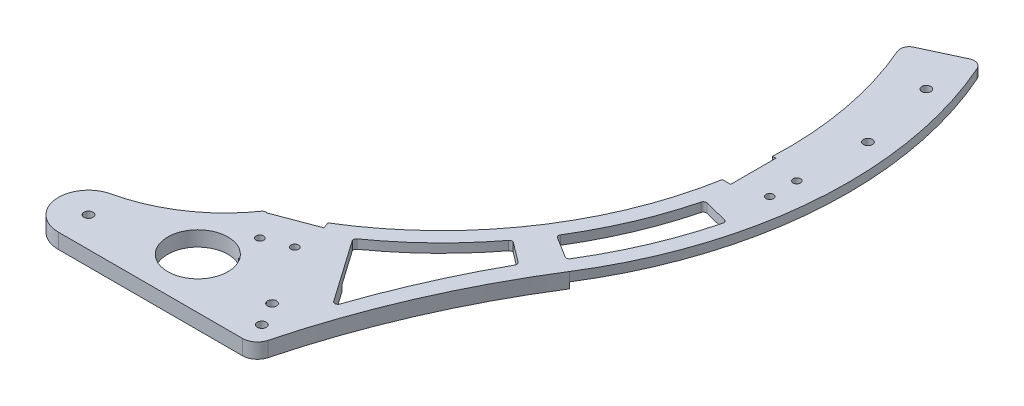
SolidWorks part; units mm, degrees
ref_plane "前视基准面" through (0, 0, 0) normal (0, 0, 1) x (1, 0, 0)
ref_plane "上视基准面" through (0, 0, 0) normal (0, 1, 0) x (1, 0, 0)
ref_plane "右视基准面" through (0, 0, 0) normal (1, 0, 0) x (0, 0, -1)
other "Configuration Table"
sketch "草图1" plane through (0, 0, 0) normal (0, 1, 0) x (1, 0, 0)
  line L0 (0, 0) -> (0, -135)
  line L1 (0, 0) -> (122.3516, 57.0535)
  line L2 (0, 0) -> (125, 0) construction
  arc A1 (0, -135) -> (122.3516, 57.0535) centre (0, 0) ccw
  dimension "D1" = 135
  dimension "D2" = 25
extrude "凸台-拉伸1" add sketch "草图1" along normal blind 3
sketch "草图2" plane through (0, 3, 0) normal (0, 1, 0) x (1, 0, 0)
  line L1 (0, 0) -> (104.2254, 48.6011)
  line L2 (122.3516, 57.0535) -> (0, 0) construction
  line L3 (0, 0) -> (54, -123.7295) construction
  line L4 (54, -123.7295) -> (46, -105.3992)
  line L5 (30, -68.7386) -> (0, -68.7386) construction
  line L7 (0, 0) -> (0, -135)
  arc A0 (46, -105.3992) -> (104.2254, 48.6011) centre (0, 0) ccw
  arc A1 (0, -135) -> (122.3516, 57.0535) centre (0, 0) ccw construction
  arc A2 (30, -68.7386) -> (67.9731, 31.6964) centre (0, 0) ccw construction
  arc A3 (0, -135) -> (54, -123.7295) centre (0, 0) ccw
  dimension "D1" = 115
  dimension "D4" = 75
  dimension "D2" = 30
extrude "切除-拉伸1" cut sketch "草图2" against normal blind 5
sketch "草图3" plane through (0, 3, 0) normal (0, 1, 0) x (1, 0, 0)
  line L0 (46, -105.3992) -> (54, -123.7295)
  line L1 (83.097, -145.3992) -> (18.097, -145.3992)
  line L2 (61.9303, -96.9001) -> (83.097, -145.3992) construction
  line L3 (8.097, -135.3992) -> (8.097, -145.3992) construction
  arc A0 (15.9052, -125.6424) -> (46, -105.3992) centre (4.9463, -76.8582) ccw
  arc A1 (15.9052, -125.6424) -> (18.097, -145.3992) centre (18.097, -135.3992) ccw
  arc A2 (114.2738, -71.8784) -> (83.097, -145.3992) centre (325.8919, -204.9864) ccw
  arc A4 (54, -123.7295) -> (114.2738, -71.8784) centre (0, 0) ccw
  arc A5 (54, -123.7295) -> (122.3516, 57.0535) centre (0, 0) ccw construction
  arc A6 (46, -105.3992) -> (104.2254, 48.6011) centre (0, 0) ccw construction
  dimension "D1" = 10
  dimension "D2" = 50
  dimension "D5" = 250
  dimension "D3" = 40
  dimension "D4" = 75
  dimension "D6" = 18
extrude "凸台-拉伸2" add sketch "草图3" against normal blind 5
sketch "草图4" plane through (0, 3, 0) normal (0, 1, 0) x (1, 0, 0)
  line L0 (0, 0) -> (135, 0) construction
  line L1 (59.9011, -97.2428) -> (60.96, -100.0497)
  line L2 (113, -5) -> (116, -5)
  line L3 (113, -5) -> (113, -20)
  line L4 (113, -20) -> (116, -20)
  line L5 (116, -5) -> (116, -20)
  line L6 (116, -5) -> (131, -5) construction
  line L7 (116, -5) -> (116, -20) construction
  line L8 (116, -20) -> (131, -20) construction
  line L9 (131, -5) -> (131, -20) construction
  line L10 (126, -8) -> (126, -17) construction
  line L11 (113, -12.5) -> (116, -12.5) construction
  line L12 (60.96, -100.0497) -> (46.9253, -105.3438)
  line L13 (46.9253, -105.3438) -> (45.8664, -102.5369)
  line L14 (45.8664, -102.5369) -> (59.9011, -97.2428)
  line L15 (46.9253, -105.3438) -> (52.2194, -119.3785) construction
  line L16 (52.2194, -119.3785) -> (66.2541, -114.0844) construction
  line L17 (66.2541, -114.0844) -> (60.96, -100.0497) construction
  line L18 (53.2616, -113.6415) -> (61.6824, -110.465) construction
  line L19 (52.8838, -99.8898) -> (53.9426, -102.6968) construction
  line L20 (122.3516, 57.0535) -> (104.2254, 48.6011) construction
  arc A0 (114.2738, -71.8784) -> (122.3516, 57.0535) centre (0, 0) ccw construction
  circle A1 centre (126, -8) radius 1.25
  circle A2 centre (126, -17) radius 1.25
  circle A3 centre (18.097, -135.3992) radius 1.5
  arc A4 (15.9052, -125.6424) -> (18.097, -145.3992) centre (18.097, -135.3992) ccw construction
  circle A5 centre (53.2616, -113.6415) radius 1.25
  circle A6 centre (61.6824, -110.465) radius 1.25
  circle A7 centre (0, 0) radius 127.5 construction
  circle A8 centre (121.091, 39.915) radius 1.5
  circle A9 centre (126.6146, 15) radius 1.5
  dimension "D8" = 2.5
  dimension "D9" = 2.5
  dimension "D11" = 3
  dimension "D13" = 2.5
  dimension "D14" = 2.5
  dimension "D18" = 255
  dimension "D19" = 3
  dimension "D20" = 3
  dimension "D1" = 3
  dimension "D2" = 15
  dimension "D3" = 15
  dimension "D4" = 5
  dimension "D5" = 113
  dimension "D6" = 9
  dimension "D7" = 4.5
  dimension "D10" = 10
  dimension "D12" = 15
  dimension "D15" = 9
  dimension "D16" = 10
  dimension "D17" = 4.5
  dimension "D21" = 15
  dimension "D22" = 15
extrude "切除-拉伸2" cut sketch "草图4" against normal blind 5
fillet "圆角1" radius 3 2 edges at (104.2254, 1.5, -48.6011) (122.3516, 1.5, -57.0535)
fillet "圆角2" radius 5 1 edges at (83.097, 0.5, 145.3992)
sketch "草图5" plane through (0, 3, 0) normal (0, 1, 0) x (1, 0, 0)
  line L0 (0, 0) -> (116.4355, -29.0306) construction
  line L1 (0, 0) -> (101.7658, -63.5903) construction
  line L2 (0, 0) -> (95.8363, -72.2178) construction
  line L3 (0, 0) -> (68.8292, -98.2982) construction
  line L4 (68.8292, -98.2982) -> (84.8893, -121.2345)
  line L5 (95.8363, -72.2178) -> (103.8226, -78.236)
  line L6 (101.7658, -63.5903) -> (110.2463, -68.8895)
  line L7 (116.4355, -29.0306) -> (126.1384, -31.4498)
  line L8 (0, 0) -> (135, 0) construction
  line L9 (0, 0) -> (90.7577, -159.7625) construction
  line L10 (32.8528, -118.3458) -> (-7.3665, -145.3992) construction
  line L11 (-7.3665, -145.3992) -> (18.097, -145.3992) construction
  line L12 (-7.3665, -145.3992) -> (47.6335, -128.6225) construction
  line L13 (6.2002, -141.261) -> (3.8905, -137.8272) construction
  line L14 (6.2002, -141.261) -> (6.2002, -145.3992) construction
  line L15 (18.097, -145.3992) -> (79.2069, -145.3992) construction
  circle A0 centre (47.6335, -128.6225) radius 10
  circle A1 centre (78.5368, -138.2497) radius 1.5
  circle A2 centre (74.0913, -130.4242) radius 1.5
  arc A5 (68.8292, -98.2982) -> (95.8363, -72.2178) centre (0, 0) ccw
  arc A6 (101.7658, -63.5903) -> (116.4355, -29.0306) centre (0, 0) ccw
  arc A7 (110.2463, -68.8895) -> (126.1384, -31.4498) centre (0, 0) ccw
  arc A9 (103.8226, -78.236) -> (84.8893, -121.2345) centre (322.145, -200.0363) ccw
  circle A10 centre (0, 0) radius 130 construction
  arc A11 (114.2738, -71.8784) -> (123.6166, 54.258) centre (0, 0) ccw construction
  arc A12 (15.9052, -125.6424) -> (46, -105.3992) centre (4.9463, -76.8582) ccw construction
  arc A15 (114.2738, -71.8784) -> (84.0439, -141.6657) centre (325.8919, -204.9864) ccw construction
  dimension "D1" = 260
  dimension "D2" = 120
  dimension "D7" = 20
  dimension "D9" = 3
  dimension "D10" = 3
  dimension "D3" = 5
  dimension "D4" = 18
  dimension "D5" = 18
  dimension "D6" = 14
  dimension "D8" = 28
  dimension "D11" = 5.4
  dimension "D12" = 9
  dimension "D13" = 150
  dimension "D14" = 55
extrude "切除-拉伸3" cut sketch "草图5" against normal blind 10
fillet "圆角3" radius 1 8 edges at (101.7658, 1.5, 63.5903) (110.2463, 1.5, 68.8895) (126.1384, 1.5, 31.4498) (116.4355, 1.5, 29.0306) (95.8363, 1.5, 72.2178) (103.8226, 1.5, 78.236) (84.8893, 0.5, 121.2345) (68.8292, 1.5, 98.2982)
